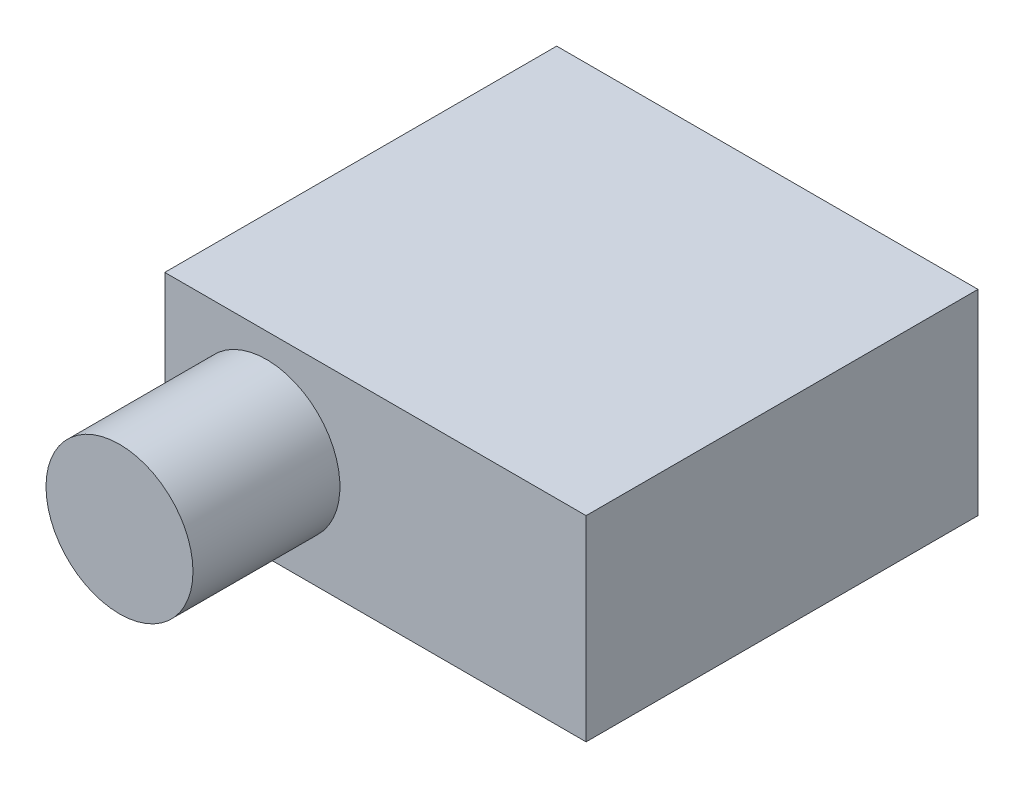
SolidWorks part; units mm, degrees
ref_plane "Front Plane" through (0, 0, 0) normal (0, 0, 1) x (1, 0, 0)
ref_plane "Top Plane" through (0, 0, 0) normal (0, 1, 0) x (1, 0, 0)
ref_plane "Right Plane" through (0, 0, 0) normal (1, 0, 0) x (0, 0, -1)
sketch "Sketch1" plane through (0, 0, 0) normal (0, 0, 1) x (1, 0, 0)
  line L1 (-21.5, -10) -> (21.5, -10)
  line L2 (-21.5, -10) -> (-21.5, 10)
  line L3 (-21.5, 10) -> (21.5, 10)
  line L4 (21.5, -10) -> (21.5, 10)
  line L5 (-21.5, -10) -> (21.5, 10) construction
  line L6 (-21.5, 10) -> (21.5, -10) construction
  point P0 (0, 0)
extrude "Boss-Extrude1" add sketch "Sketch1" along normal blind 40
sketch "Sketch2" plane through (0, 0, 40) normal (0, 0, 1) x (1, 0, 0)
  circle A0 centre (-11.1223, 0) radius 7.5
extrude "Boss-Extrude2" add sketch "Sketch2" along normal blind 15
